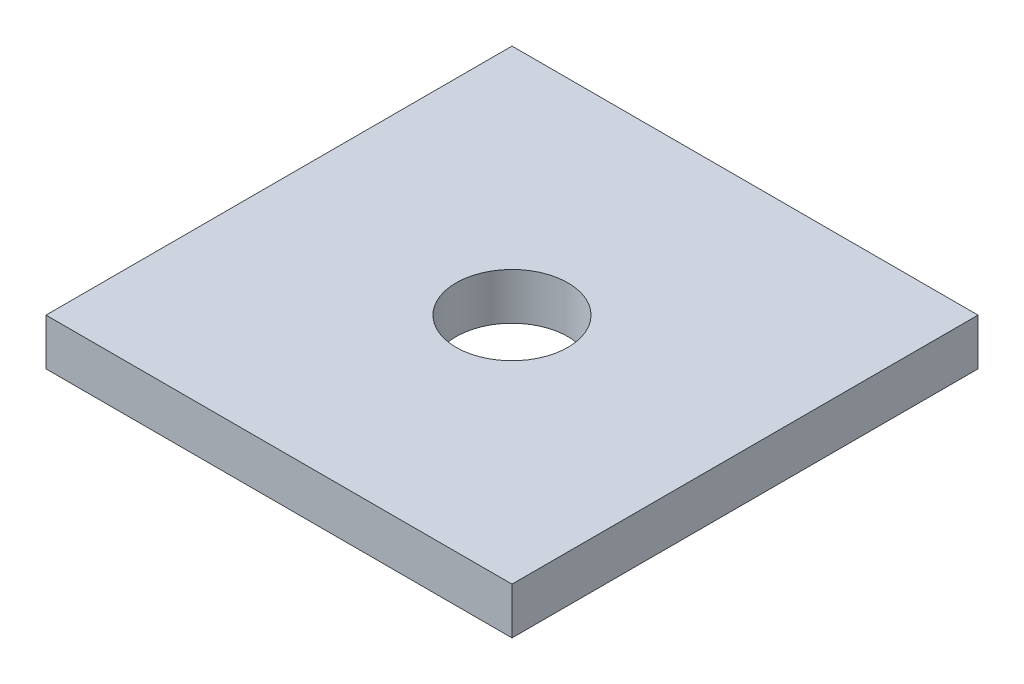
SolidWorks part; units mm, degrees
ref_plane "Спереди" through (0, 0, 0) normal (0, 0, 1) x (1, 0, 0)
ref_plane "Сверху" through (0, 0, 0) normal (0, 1, 0) x (1, 0, 0)
ref_plane "Справа" through (0, 0, 0) normal (1, 0, 0) x (0, 0, -1)
sketch "Эскиз1" plane through (0, 0, 0) normal (0, 1, 0) x (1, 0, 0)
  line L1 (0, 0) -> (50, 0)
  line L2 (0, 0) -> (0, 50)
  line L3 (0, 50) -> (50, 50)
  line L4 (50, 0) -> (50, 50)
  circle A0 centre (25, 25) radius 6
extrude "Бобышка-Вытянуть1" add sketch "Эскиз1" along normal blind 5
